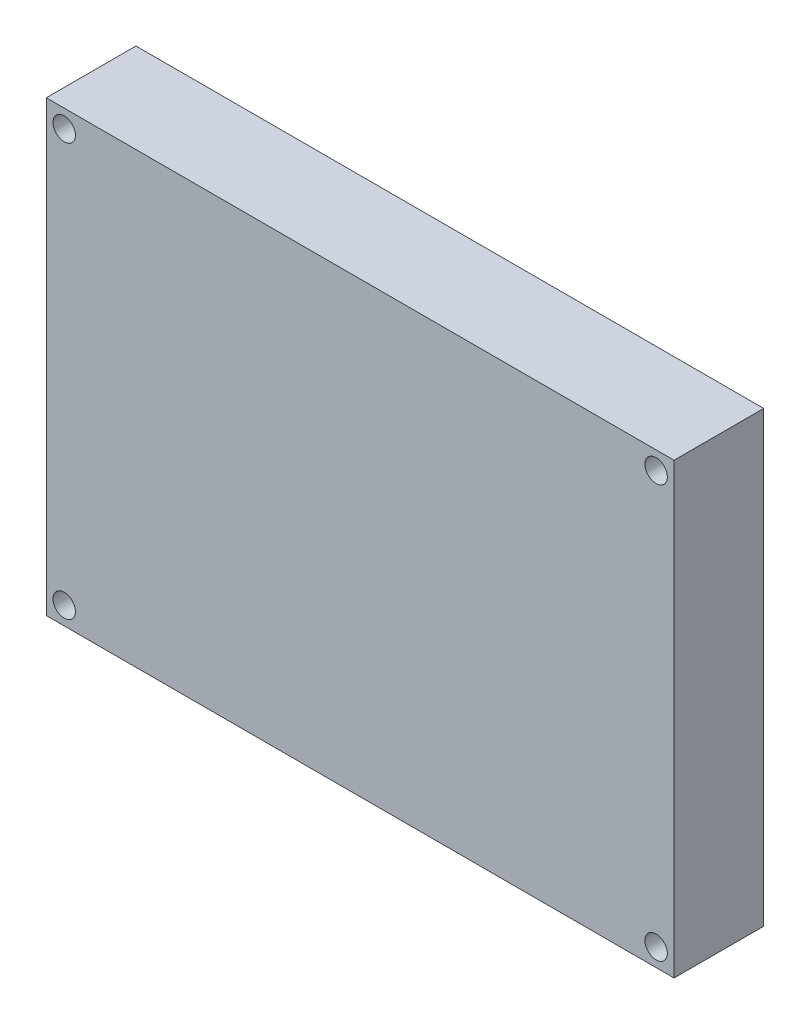
SolidWorks part; units mm, degrees
ref_plane "Piano frontale" through (0, 0, 0) normal (0, 0, 1) x (1, 0, 0)
ref_plane "Piano superiore" through (0, 0, 0) normal (0, 1, 0) x (1, 0, 0)
ref_plane "Piano destro" through (0, 0, 0) normal (1, 0, 0) x (0, 0, -1)
sketch "Schizzo1" plane through (0, 0, 0) normal (0, 0, 1) x (1, 0, 0)
  line L1 (-35, 25) -> (35, 25)
  line L2 (-35, 25) -> (-35, -25)
  line L3 (-35, -25) -> (35, -25)
  line L4 (35, 25) -> (35, -25)
  line L5 (-35, 25) -> (35, -25) construction
  line L6 (-35, -25) -> (35, 25) construction
  point P0 (0, 0)
  dimension "D1" = 50
  dimension "D2" = 70
extrude "Estrusione-Estrusione1" add sketch "Schizzo1" along normal blind 10
sketch "Schizzo2" plane through (0, 0, 10) normal (0, 0, 1) x (1, 0, 0)
  line L0 (-35, 25) -> (-35, -25) construction
  line L1 (35, 25) -> (-35, 25) construction
  line L2 (0, 30.1661) -> (0, -31.0602) construction
  line L3 (-47.7692, 0) -> (50.2666, 0) construction
  circle A0 centre (-33, 23) radius 1.25
  circle A1 centre (33, 23) radius 1.25
  circle A2 centre (33, -23) radius 1.25
  circle A3 centre (-33, -23) radius 1.25
  dimension "D1" = 2.5
  dimension "D2" = 2
  dimension "D3" = 2
extrude "Taglio-Estrusione1" cut sketch "Schizzo2" against normal through all
